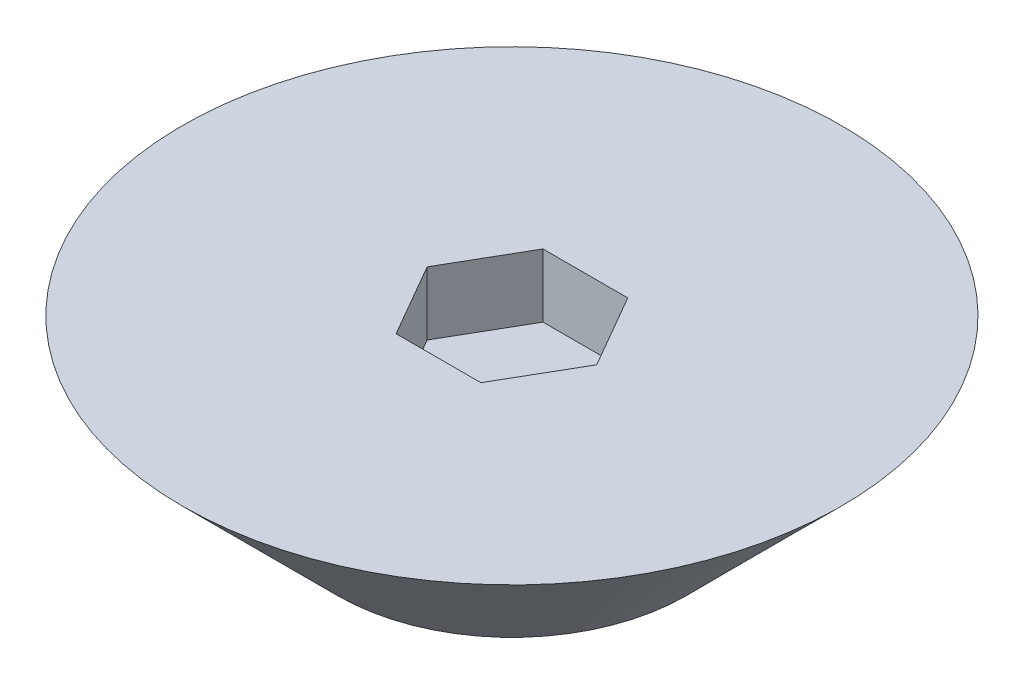
SolidWorks part; units mm, degrees
ref_plane "Front Plane" through (0, 0, 0) normal (0, 0, 1) x (1, 0, 0)
ref_plane "Top Plane" through (0, 0, 0) normal (0, 1, 0) x (1, 0, 0)
ref_plane "Right Plane" through (0, 0, 0) normal (1, 0, 0) x (0, 0, -1)
ref_plane "Plane1" through (0, 2.45, 0) normal (0, 1, 0) x (1, 0, 0)
sketch "Sketch4" plane through (0, 2.45, 0) normal (0, 1, 0) x (1, 0, 0)
  circle A0 centre (0, 0) radius 5.2
sketch "Sketch5" plane through (0, 0, 0) normal (0, 1, 0) x (1, 0, 0)
  circle A0 centre (0, 0) radius 2.75
loft "Loft1" add profiles "Sketch5", "Sketch4"
sketch "Sketch6" plane through (0, 2.45, 0) normal (0, 1, 0) x (1, 0, 0)
  line L1 (1.338, 0) -> (0.669, 1.1587)
  line L2 (0.669, 1.1587) -> (-0.669, 1.1587)
  line L3 (-0.669, 1.1587) -> (-1.338, 0)
  line L4 (-1.338, 0) -> (-0.669, -1.1587)
  line L5 (-0.669, -1.1587) -> (0.669, -1.1587)
  line L6 (0.669, -1.1587) -> (1.338, 0)
  circle A0 centre (0, 0) radius 1.1587 construction
extrude "Cut-Extrude1" cut sketch "Sketch6" against normal blind 1
